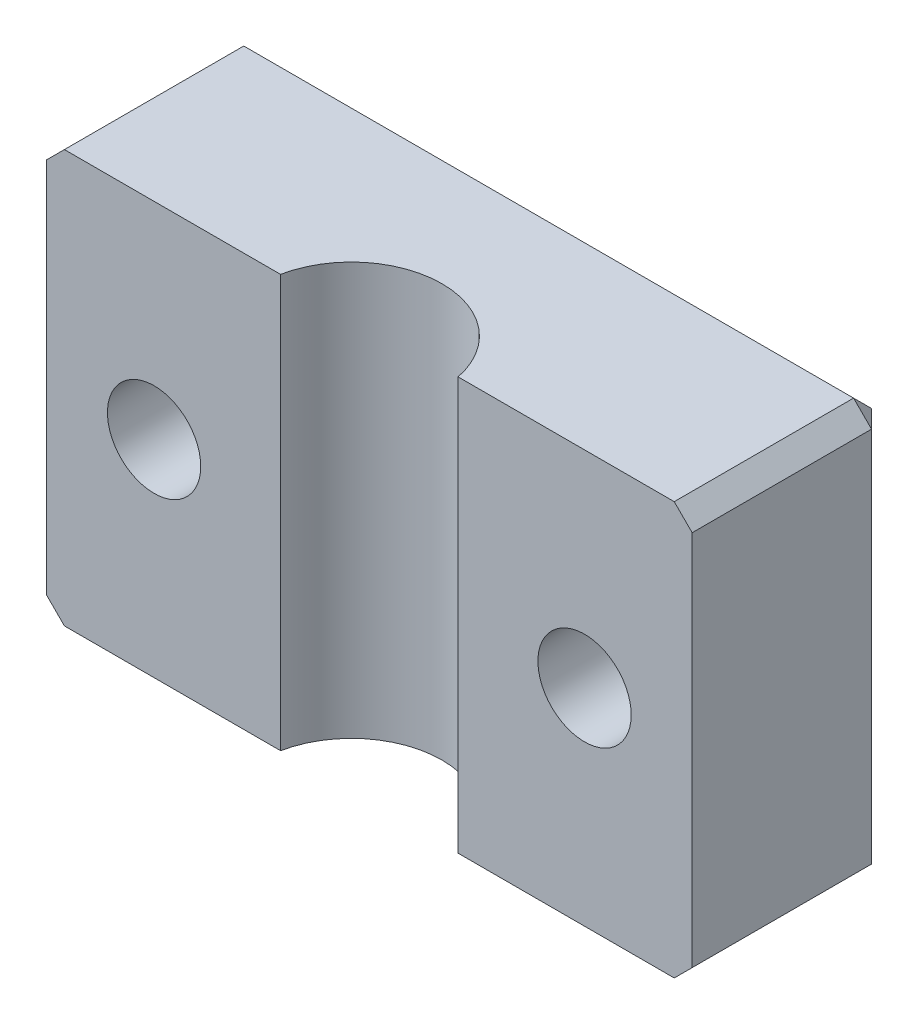
SolidWorks part; units mm, degrees
material "ABS"
ref_plane "Front Plane" through (0, 0, 0) normal (0, 0, 1) x (1, 0, 0)
ref_plane "Top Plane" through (0, 0, 0) normal (0, 1, 0) x (1, 0, 0)
ref_plane "Right Plane" through (0, 0, 0) normal (1, 0, 0) x (0, 0, -1)
sketch "Sketch1" plane through (0, 0, 0) normal (0, 1, 0) x (1, 0, 0)
  line L0 (-18, 0) -> (18, 0)
  line L1 (18, 0) -> (18, -11)
  line L2 (18, -11) -> (4.95, -11)
  line L3 (-18, -11) -> (-18, 0)
  line L4 (0, 0) -> (0, -10) construction
  line L5 (-4.95, -11) -> (-18, -11)
  arc A0 (4.95, -11) -> (-4.95, -11) centre (0, -12) ccw
  dimension "D2" = 1
  dimension "D3" = 10.1
  dimension "D1" = 36
  dimension "D4" = 11
extrude "Boss-Extrude1" add sketch "Sketch1" along normal blind 23
sketch "Sketch2" plane through (0, 0, 11) normal (0, 0, 1) x (1, 0, 0)
  line L0 (0, 23) -> (0, 0) construction
  line L1 (4.95, 23) -> (-4.95, 23) construction
  line L2 (-18, 11.5) -> (18, 11.5) construction
  line L3 (-18, 23) -> (-18, 0) construction
  line L4 (18, 23) -> (18, 0) construction
  circle A0 centre (-12, 11.5) radius 2.6
  circle A1 centre (12, 11.5) radius 2.6
  dimension "D1" = 5.2
  dimension "D2" = 12
extrude "Cut-Extrude1" cut sketch "Sketch2" against normal up to next
chamfer "Chamfer1" distance 1 angle 45 8 edges at (18, 0, 5.5) (-18, 0, 5.5) (-18, 23, 5.5) (18, 23, 5.5) (-18, 11.5, 0) (0, 0, 0) (18, 11.5, 0) (0, 23, 0)
